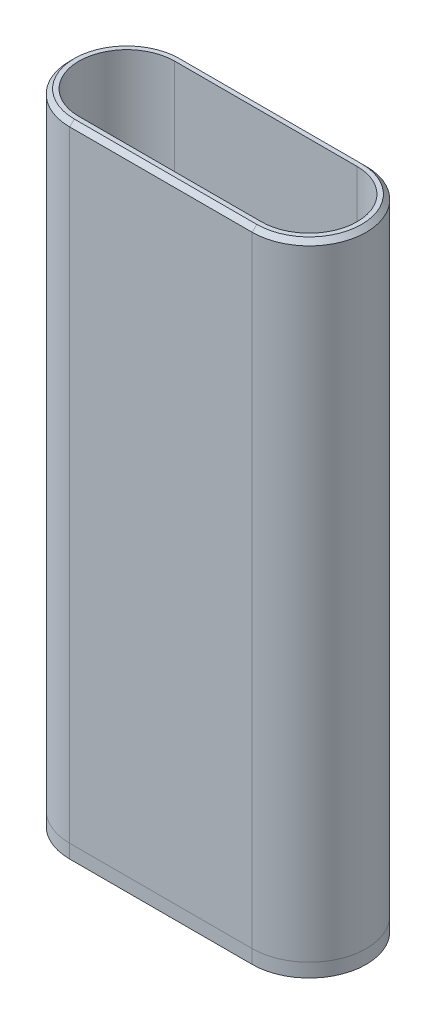
SolidWorks part; units mm, degrees
ref_plane "Front Plane" through (0, 0, 0) normal (0, 0, 1) x (1, 0, 0)
ref_plane "Top Plane" through (0, 0, 0) normal (0, 1, 0) x (1, 0, 0)
ref_plane "Right Plane" through (0, 0, 0) normal (1, 0, 0) x (0, 0, -1)
sketch "Sketch2" plane through (0, 12, 0) normal (0, -1, 0) x (1, 0, 0)
  line L8 (5.45, 3.45) -> (5.45, -3.45) construction
  line L9 (-7.45, -5.65) -> (7.45, -5.65)
  line L10 (-7.45, -5.65) -> (-7.45, 5.65)
  line L11 (-7.45, 5.65) -> (7.45, 5.65)
  line L12 (4.15, -3.65) -> (4.15, 3.65)
  line L13 (4.15, 3.65) -> (-4.15, 3.65)
  line L14 (-4.15, 3.65) -> (-4.15, -3.65)
  line L15 (-4.15, -3.65) -> (4.15, -3.65)
  line L16 (4.15, -3.65) -> (4.15, 3.65)
  line L17 (4.15, 3.65) -> (-4.15, 3.65)
  line L18 (-4.15, 3.65) -> (-4.15, -3.65)
  line L19 (-4.15, -3.65) -> (4.15, -3.65)
  line L20 (7.45, -5.65) -> (7.45, 5.65)
  line L21 (0, 5.65) -> (0, -5.65) construction
  line L22 (-7.45, 0) -> (7.45, 0) construction
  point P0 (0, 0)
  dimension "D2" = 2
  dimension "D3" = 2
  dimension "D4" = 8.3
  dimension "D5" = 7.3
  dimension "D1" = 0.2
extrude "Boss-Extrude1" add sketch "Sketch2" along normal offset from surface (12.6 mm away) 0.6
sketch "Sketch4" plane through (0, 0, 0) normal (1, 0, 0) x (0, 0, -1)
  line L1 (-1.6, 9.8) -> (-1.6, 8) construction
  line L2 (1.6, 8) -> (1.6, 9.8) construction
  line L3 (2.75, 8) -> (1.6, 8) construction
  line L4 (-1.6, 8) -> (-2.75, 8) construction
  line L5 (-2.75, 8) -> (-2.75, 12) construction
  line L6 (-2.75, 12) -> (-3.45, 12) construction
  line L7 (-3.45, 12) -> (-3.45, 0) construction
  line L8 (-3.45, 0) -> (3.45, 0) construction
  line L9 (3.45, 0) -> (3.45, 12) construction
  line L10 (3.45, 12) -> (2.75, 12) construction
  line L11 (2.75, 12) -> (2.75, 8) construction
  line L13 (-1.6, 9.8) -> (-1.6, 8) construction
  line L14 (1.6, 8) -> (1.6, 9.8) construction
  line L15 (2.75, 8) -> (1.6, 8) construction
  line L16 (-1.6, 8) -> (-2.75, 8) construction
  line L17 (-2.75, 8) -> (-2.75, 12) construction
  line L18 (-2.75, 12) -> (-3.45, 12) construction
  line L19 (-3.45, 12) -> (-3.45, 0) construction
  line L20 (-3.45, 0) -> (3.45, 0) construction
  line L21 (3.45, 0) -> (3.45, 12) construction
  line L22 (3.45, 12) -> (2.75, 12) construction
  line L23 (2.75, 12) -> (2.75, 8) construction
  line L24 (0, -990) -> (0, 49010) construction
  line L25 (-2.3, 10.1) -> (2.3, 10.1)
  line L26 (-2.3, 10.1) -> (-2.3, 7)
  line L27 (-2.3, 7) -> (2.3, 7)
  line L28 (1.6, 10) -> (-1.6, 10)
  line L29 (-1.6, 10) -> (-1.6, 9.8)
  line L30 (-1.6, 9.8) -> (1.6, 9.8)
  line L31 (1.6, 9.8) -> (1.6, 10)
  line L32 (1.6, 10) -> (-1.6, 10) construction
  line L33 (-1.6, 10) -> (-1.6, 9.8) construction
  line L34 (2.3, 10.1) -> (2.3, 7)
  line L35 (1.6, 9.8) -> (1.6, 10) construction
  point P20 (0, 10)
  dimension "D2" = 0.7
  dimension "D3" = 0.1
  dimension "D4" = 1
  dimension "D1" = 0
extrude "Cut-Extrude1" cut sketch "Sketch4" against normal through all both and the other way through all contours L25 L34 L27 L26
sketch "Sketch5" plane through (0, -0.6, 0) normal (0, -1, 0) x (1, 0, 0)
  line L0 (-20, 0) -> (20, 0) construction
  line L1 (-20, 12.5) -> (20, 12.5)
  line L2 (-20, -12.5) -> (20, -12.5)
  arc A0 (-20, 12.5) -> (-20, -12.5) centre (-20, 0) ccw
  arc A1 (20, -12.5) -> (20, 12.5) centre (20, 0) ccw
  point P2 (0, 0)
  dimension "D1" = 25
  dimension "D2" = 40
extrude "Boss-Extrude2" add sketch "Sketch5" along normal blind 3
sketch "Sketch7" plane through (0, -0.6, 0) normal (0, 1, 0) x (1, 0, 0)
  line L0 (-20, -10.5) -> (20, -10.5)
  line L1 (20, 10.5) -> (-20, 10.5)
  line L2 (-20, -12.5) -> (20, -12.5)
  line L3 (20, 12.5) -> (-20, 12.5)
  line L4 (-20, -12.5) -> (20, -12.5)
  line L5 (20, 12.5) -> (-20, 12.5)
  arc A0 (20, -10.5) -> (20, 10.5) centre (20, 0) ccw
  arc A1 (-20, 10.5) -> (-20, -10.5) centre (-20, 0) ccw
  arc A2 (-20, 12.5) -> (-20, -12.5) centre (-20, 0) ccw
  arc A3 (20, -12.5) -> (20, 12.5) centre (20, 0) ccw
  arc A4 (-20, 12.5) -> (-20, -12.5) centre (-20, 0) ccw
  arc A5 (20, -12.5) -> (20, 12.5) centre (20, 0) ccw
  dimension "D1" = 0
  dimension "D2" = 2
extrude "Boss-Extrude3" add sketch "Sketch7" along normal blind 137 separate body
sketch "Sketch8" plane through (0, -0.6, 0) normal (0, -1, 0) x (1, 0, 0)
  line L0 (-7.45, -5.65) -> (7.45, -5.65) construction
  line L1 (-7.45, 5.65) -> (-7.45, -5.65) construction
  line L2 (7.45, 5.65) -> (-7.45, 5.65) construction
  line L3 (7.45, -5.65) -> (7.45, 5.65) construction
  line L4 (-7.45, -5.65) -> (7.45, -5.65) construction
  line L5 (-7.45, 5.65) -> (-7.45, -5.65) construction
  line L6 (7.45, 5.65) -> (-7.45, 5.65) construction
  line L7 (7.45, -5.65) -> (7.45, 5.65) construction
  line L12 (20, -12.5) -> (-20, -12.5) construction
  line L13 (-20, 12.5) -> (20, 12.5) construction
  line L14 (20, -12.5) -> (-20, -12.5)
  line L15 (-20, 12.5) -> (20, 12.5)
  line L17 (-14.45, 7.65) -> (14.45, 7.65)
  line L18 (-14.45, 7.65) -> (-14.45, -7.65)
  line L19 (-14.45, -7.65) -> (14.45, -7.65)
  line L20 (14.45, 7.65) -> (14.45, -7.65)
  arc A0 (20, -12.5) -> (20, 12.5) centre (20, 0) ccw construction
  arc A1 (-20, 12.5) -> (-20, -12.5) centre (-20, 0) ccw construction
  arc A2 (20, -12.5) -> (20, 12.5) centre (20, 0) ccw
  arc A3 (-20, 12.5) -> (-20, -12.5) centre (-20, 0) ccw
  dimension "D1" = 2
  dimension "D2" = 2
  dimension "D3" = 7
  dimension "D4" = 7
extrude "Boss-Extrude4" add sketch "Sketch8" against normal blind 7.2
sketch "Sketch9" plane through (0, -0.6, 0) normal (0, -1, 0) x (1, 0, 0)
  line L0 (-20, 0) -> (20, 0) construction
  point P4 (0, 0)
  dimension "D1" = 40
hole_wizard "M3 Clearance Hole1" positions "Sketch10" profile "Sketch11" hole size "M3" standard "ANSI Metric" end condition through all
sketch "Sketch10" plane through (0, -0.6, 0) normal (0, -1, 0) x (-1, 0, 0)
  point P0 (20, 0)
  point P3 (-20, 0)
sketch "Sketch11" plane through (-20, -0.6, 0) normal (1, 0, 0) x (0, 0, -1)
  line L0 (0, 0) -> (0, 137)
  line L1 (0, 137) -> (1.8, 137)
  line L2 (1.8, 137) -> (1.8, 0)
  line L5 (1.8, 0) -> (0, 0)
  line L11 (0, -6.35) -> (0, 107.95) construction
  dimension "Thru Hole Dia." = 3.6
  dimension "Thru Hole Depth" = 137
ref_plane "Plane1" through (0, 1.4, 0) normal (0, 1, 0) x (1, 0, 0)
sketch "Sketch13" plane through (0, 1.4, 0) normal (0, 1, 0) x (1, 0, 0)
  line L0 (-18.3546, 2.85) -> (-14.45, 2.85)
  line L1 (-18.3546, 2.85) -> (-21.6454, 2.85)
  line L2 (-21.6454, 2.85) -> (-23.2909, 0)
  line L3 (-23.2909, 0) -> (-21.6454, -2.85)
  line L4 (-21.6454, -2.85) -> (-18.3546, -2.85)
  line L5 (-18.3546, -2.85) -> (-16.7091, 0)
  line L6 (-16.7091, 0) -> (-18.3546, 2.85)
  line L13 (-14.45, -7.65) -> (-14.45, 7.65) construction
  line L14 (-14.45, 2.85) -> (-14.45, -2.85)
  line L15 (-14.45, -2.85) -> (-18.3546, -2.85)
  circle A0 centre (-20, 0) radius 2.85 construction
  dimension "D1" = 5.7
extrude "Cut-Extrude2" cut sketch "Sketch13" along normal blind 3 contours L15 L14 L0 L6 L5 | L5 L6 L1 L2 L3 L4
sketch "Sketch14" plane through (0, 4.4, 0) normal (0, -1, 0) x (1, 0, 0)
  line L0 (-14.45, 2.85) -> (-21.6454, 2.85) construction
  line L1 (-21.8, 2.85) -> (-18.2, 2.85)
  line L2 (-21.8, 2.85) -> (-21.8, -2.85)
  line L3 (-21.8, -2.85) -> (-18.2, -2.85)
  line L4 (-18.2, 2.85) -> (-18.2, -2.85)
  line L5 (-21.6454, -2.85) -> (-14.45, -2.85) construction
  line L6 (-21.8, 2.5823) -> (-21.6454, 2.85)
  line L7 (-23.2909, 0) -> (-21.6454, 2.85) construction
  line L8 (-21.8, -2.5823) -> (-21.6454, -2.85)
  line L9 (-21.6454, -2.85) -> (-23.2909, 0) construction
  circle A0 centre (-20, 0) radius 1.8 construction
  line M5 (-21.6454, -2.85) -> (-14.45, -2.85)
  line M7 (-14.45, 2.85) -> (-21.6454, 2.85)
  line M8 (-21.6454, 2.85) -> (-23.2909, 0)
  line M9 (-23.2909, 0) -> (-21.6454, -2.85)
  circle M10 centre (-20, 0) radius 1.8
extrude "Cut-Extrude3" cut sketch "Sketch14" against normal blind 0.3 contours L4 L2 M10 M9 M5 | L4 L2 M7 M8 M10
sketch "Sketch15" plane through (0, 4.7, 0) normal (0, -1, 0) x (1, 0, 0)
  line L0 (-21.8, 2.5823) -> (-21.8, 0) construction
  line L1 (-18.2, -1.8) -> (-21.8, -1.8)
  line L2 (-18.2, -1.8) -> (-18.2, 1.8)
  line L3 (-18.2, 1.8) -> (-21.8, 1.8)
  line L4 (-21.8, -1.8) -> (-21.8, 1.8)
  line L5 (-18.2, 2.85) -> (-18.2, 0) construction
  arc A0 (-18.2, 0) -> (-21.8, 0) centre (-20, 0) ccw construction
  arc A1 (-21.8, 0) -> (-18.2, 0) centre (-20, 0) ccw construction
extrude "Cut-Extrude4" cut sketch "Sketch15" against normal blind 0.3
chamfer "Chamfer1" distance 1 angle 45 4 edges at (32.5, 136.4, 0) (0, 136.4, -12.5) (0, 136.4, 12.5) (-32.5, 136.4, 0)
mirror "Mirror1" about plane through (0, 0, 0) normal (1, 0, 0) of "Cut-Extrude4", "Cut-Extrude3", "Cut-Extrude2"
chamfer "Chamfer2" distance 1.5 angle 45 4 edges at (-14.45, -0.6, 0) (0, -0.6, 7.65) (14.45, -0.6, 0) (0, -0.6, -7.65)
equation "\"case_length\"= 140"
equation "\"plate_thickness\"= 3"
equation "\"D1@Boss-Extrude2\"=\"plate_thickness\""
equation "\"D1@Boss-Extrude3\"=\"case_length\"-\"plate_thickness\""
equation "\"case_height\"= 25"
equation "\"case_width\"= 65"
equation "\"case_to_shell_offset\"= 19.6"
equation "\"body_tip_distance\"= 30"
equation "\"D2@Sketch5\"=\"case_width\"-\"case_height\""
equation "\"D1@Sketch5\"=\"case_height\""
equation "\"D1@Sketch9\"= \"case_width\" - \"case_height\""
equation "\"D2@Sketch8\"=\"D1@Sketch8\""
equation "\"D4@Sketch8\"=\"D3@Sketch8\""
